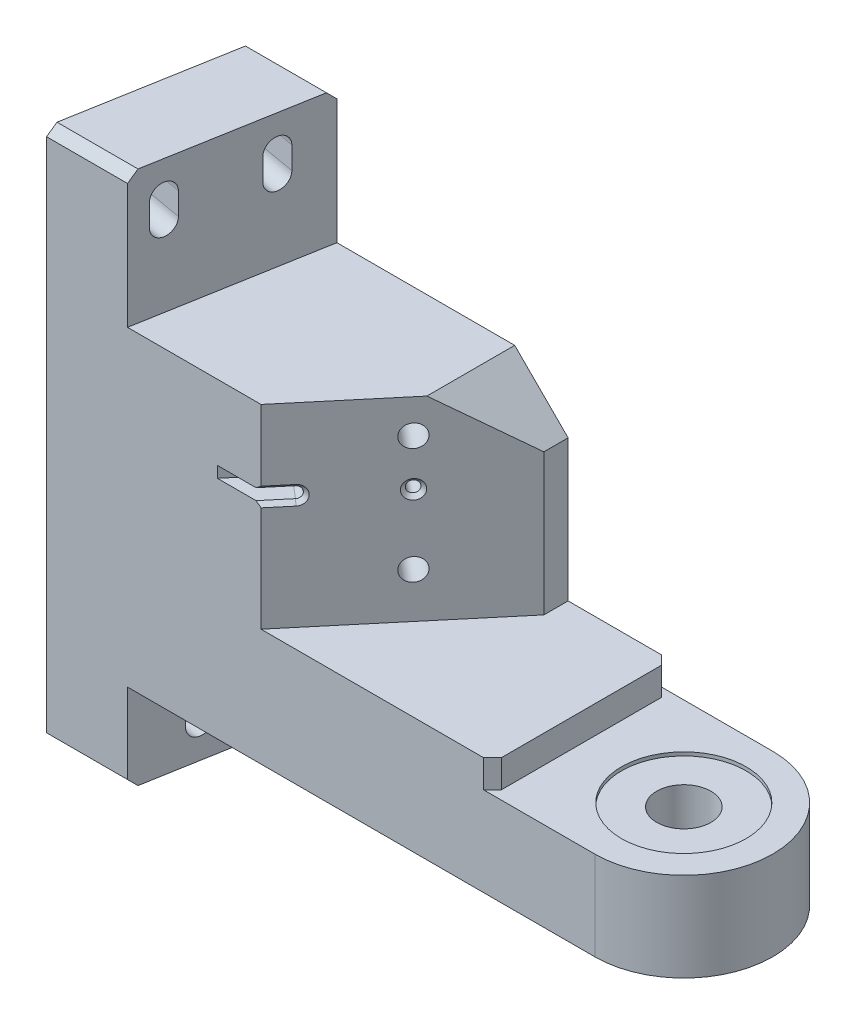
SolidWorks part; units mm, degrees
material "6061-T6 Al"
ref_plane "Front" through (0, 0, 0) normal (0, 0, 1) x (1, 0, 0)
ref_plane "Top" through (0, 0, 0) normal (0, 1, 0) x (1, 0, 0)
ref_plane "Right" through (0, 0, 0) normal (1, 0, 0) x (0, 0, -1)
sketch "Sketch1" plane through (0, 0, 0) normal (0, 1, 0) x (1, 0, 0)
  line L0 (-156.464, 0) -> (25.4, 0) construction
  line L1 (-156.464, 25.4) -> (25.4, 25.4)
  line L2 (-156.464, 25.4) -> (-156.464, -25.4)
  line L3 (-156.464, -25.4) -> (25.4, -25.4)
  line L4 (25.4, 25.4) -> (25.4, -25.4)
  dimension "D1" = 25.4
  dimension "D2" = 181.864
  dimension "D3" = 50.8
extrude "Extrude1" add sketch "Sketch1" along normal blind 152.4
sketch "Sketch2" plane through (0, 152.4, 0) normal (0, 1, 0) x (1, 0, 0)
  line L0 (-156.464, -25.4) -> (-156.464, 25.4)
  line L1 (-156.464, 25.4) -> (-147.5066, 25.4)
  line L2 (25.4, 25.4) -> (-156.464, 25.4) construction
  line L3 (-147.5066, 25.4) -> (-156.464, -25.4)
  dimension "D1" = 10
extrude "Extrude2" cut sketch "Sketch2" against normal through all
sketch "Sketch3" plane through (0, 152.4, 0) normal (0, 1, 0) x (1, 0, 0)
  line L0 (25.4, -25.4) -> (25.4, 25.4) construction
  line L1 (-156.464, -25.4) -> (25.4, -25.4) construction
  line L2 (25.4, 25.4) -> (-147.5066, 25.4) construction
  line L3 (25.4, -25.4) -> (25.4, 25.4)
  line L4 (-133.35, -25.4) -> (25.4, -25.4)
  line L5 (25.4, 25.4) -> (-124.3926, 25.4)
  line L6 (-124.3926, 25.4) -> (-133.35, -25.4)
  line L7 (-156.464, -25.4) -> (-147.5066, 25.4) construction
  dimension "D1" = 133.35
extrude "Extrude3" cut sketch "Sketch3" against normal blind 38.1
sketch "Sketch4" plane through (0, 114.3, 0) normal (0, 1, 0) x (1, 0, 0)
  line L1 (-133.35, -25.4) -> (25.4, -25.4) construction
  line L2 (25.4, 25.4) -> (-124.3926, 25.4) construction
  line L3 (25.4, -25.4) -> (25.4, 25.4) construction
  line L4 (25.4, -25.4) -> (-95.25, -25.4)
  line L5 (-58.42, 25.4) -> (25.4, 25.4)
  line L6 (-58.42, 25.4) -> (-58.42, 18.4923)
  line L7 (-58.42, 18.4923) -> (-95.25, -25.4)
  line L8 (25.4, -25.4) -> (25.4, 25.4)
  dimension "D1" = 130
  dimension "D2" = 58.42
  dimension "D3" = 95.25
extrude "Extrude4" cut sketch "Sketch4" against normal blind 55.5498
sketch "Sketch5" plane through (0, 58.7502, 0) normal (0, 1, 0) x (1, 0, 0)
  line L0 (-95.25, -25.4) -> (25.4, -25.4) construction
  line L1 (25.4, -25.4) -> (25.4, 25.4) construction
  line L2 (25.4, 25.4) -> (-58.42, 25.4) construction
  line L3 (-29.21, -25.4) -> (25.4, -25.4)
  line L4 (25.4, -25.4) -> (25.4, 25.4)
  line L5 (25.4, 25.4) -> (-29.21, 25.4)
  line L6 (-29.21, 25.4) -> (-29.21, -25.4)
  dimension "D1" = 29.21
extrude "Extrude5" cut sketch "Sketch5" against normal blind 7.9502
sketch "Sketch6" plane through (0, 0, 0) normal (0, -1, 0) x (1, 0, 0)
  line L0 (25.4, 25.4) -> (25.4, -25.4) construction
  line L1 (25.4, -25.4) -> (-147.5066, -25.4) construction
  line L2 (-156.464, 25.4) -> (25.4, 25.4) construction
  line L3 (25.4, 25.4) -> (25.4, -25.4)
  line L4 (25.4, -25.4) -> (-124.3926, -25.4)
  line L5 (-133.35, 25.4) -> (25.4, 25.4)
  line L7 (-124.3926, -25.4) -> (-133.35, 25.4)
extrude "Extrude6" cut sketch "Sketch6" against normal blind 25.4
sketch "Sketch7" plane through (-124.9853, 0, -22.0383) normal (0.9848, 0, 0.1736) x (0.1736, 0, -0.9848)
  line L0 (-39.2044, 142.9766) -> (-39.2044, 136.6266) construction
  line L1 (-35.6357, 142.9766) -> (-35.6357, 136.6266)
  line L2 (-42.7731, 142.9766) -> (-42.7731, 136.6266)
  line L3 (-48.1701, 0) -> (3.4136, 0) construction
  line L4 (-52.1838, 152.4) -> (-52.1838, 0) construction
  arc A0 (-35.6357, 142.9766) -> (-42.7731, 142.9766) centre (-39.2044, 142.9766) ccw
  arc A1 (-42.7731, 136.6266) -> (-35.6357, 136.6266) centre (-39.2044, 136.6266) ccw
  circle A2 centre (-39.2044, 139.8016) radius 3.5687 construction
  point P2 (-39.2044, 139.8016)
  dimension "D1" = 7.1374
  dimension "D2" = 6.35
  dimension "D3" = 139.8016
  dimension "D4" = 12.9794
extrude "Extrude7" cut sketch "Sketch7" against normal through all
pattern_linear "LPattern1" count 2 spacing 127 along (0, -1, 0) count 2 spacing 27.94 along (0.1736, 0, -0.9848) skipping (1, 0) of "Extrude7"
hole_wizard "1/4-20 Tapped Hole1" positions "Sketch9" profile "Sketch8" tap size "1/4-20" standard "Ansi Inch"
sketch "Sketch9" plane through (-43.3879, 0, -36.4068) normal (0.766, 0, 0.6428) x (0.6428, 0, -0.766)
  line L0 (-3.1307, 25.4) -> (-105.1733, 25.4) construction
  line L4 (-80.683, 58.7502) -> (-80.683, 114.3) construction
  point P0 (-49.822, 104.648)
  point P2 (-49.822, 71.628)
  dimension "D1" = 33.02
  dimension "D2" = 46.228
  dimension "D3" = 30.861
sketch "Sketch8" plane through (-75.4129, 104.648, 1.7591) normal (0, 1, 0) x (0.6428, 0, -0.766)
  line L0 (0, 0) -> (0, 18.0438)
  line L1 (0, 18.0438) -> (2.5527, 16.51)
  line L2 (2.5527, 16.51) -> (2.5527, 12.7)
  line L3 (2.5527, 12.7) -> (3.175, 12.7)
  line L4 (3.175, 12.7) -> (3.175, 0)
  line L5 (3.175, 0) -> (0, 0)
  line L10 (0, 18.0438) -> (-2.5527, 16.51) construction
  line L11 (0, -6.35) -> (0, 107.95) construction
  dimension "Tap Drill Dia." = 5.1054
  dimension "Tap Drill Depth" = 16.51
  dimension "Thread Major Dia." = 6.35
  dimension "Thread Depth" = 12.7
  dimension "Drill Angle" = 118
sketch "Sketch19" plane through (0, 25.4, 0) normal (0, -1, 0) x (1, 0, 0)
  line L4 (25.4, 25.4) -> (-133.35, 25.4)
  line L5 (-133.35, 25.4) -> (-124.3926, -25.4)
  line L6 (-124.3926, -25.4) -> (25.4, -25.4)
  line L7 (25.4, -25.4) -> (25.4, 25.4)
  line L8 (27.94, 25.4) -> (0, 25.4)
  line L10 (0, -25.4) -> (27.94, -25.4)
  line L11 (27.94, -25.4) -> (27.94, 25.4)
  arc A0 (0, -25.4) -> (0, 25.4) centre (0, 0) ccw
  dimension "D2" = 25.4
  dimension "D3" = 27.94
  dimension "D4" = 50.8
  dimension "D1" = 0
extrude "Extrude9" cut sketch "Sketch19" against normal through all
chamfer "Chamfer1" distance 2.54 angle 45 6 edges at (-29.21, 54.7751, 25.4) (-29.21, 54.7751, -25.4) (-135.9496, 152.4, -25.4) (-135.9496, 0, -25.4) (-144.907, 0, 25.4) (-144.907, 152.4, 25.4)
chamfer "Chamfer2" distance 15.24 angle 45 1 edges at (-58.42, 114.3, -21.9461)
sketch "Sketch20" plane through (-124.9853, 0, -22.0383) normal (0.9848, 0, 0.1736) x (0.1736, 0, -0.9848)
  line L0 (-30.3144, 15.9766) -> (-30.3144, 9.6266) construction
  line L1 (-26.7457, 15.9766) -> (-26.7457, 9.6266)
  line L2 (-33.8831, 15.9766) -> (-33.8831, 9.6266)
  line L3 (-11.2644, 9.6266) -> (-30.3144, 9.6266) construction
  line L4 (-11.2644, 15.9766) -> (-30.3144, 15.9766) construction
  arc A0 (-26.7457, 15.9766) -> (-33.8831, 15.9766) centre (-30.3144, 15.9766) ccw
  arc A1 (-33.8831, 9.6266) -> (-26.7457, 9.6266) centre (-30.3144, 9.6266) ccw
  arc A2 (-14.8331, 9.6266) -> (-7.6957, 9.6266) centre (-11.2644, 9.6266) ccw construction
  point P2 (-30.3144, 12.8016)
  dimension "D1" = 19.05
extrude "Extrude10" cut sketch "Sketch20" against normal through all
hole_wizard "SCREW THRU HOLE AND CBORE" positions "Sketch22" profile "Sketch21" counterbore size "5/8" standard "Ansi Inch" end condition through all
sketch "Sketch22" plane through (0, 50.8, 0) normal (0, 1, 0) x (-1, 0, 0)
  point P0 (0, 0)
sketch "Sketch21" plane through (0, 50.8, 0) normal (1, 0, 0) x (0, 0, 1)
  line L0 (0, 0) -> (0, 50.8)
  line L1 (0, 50.8) -> (7.7343, 50.8)
  line L3 (7.7343, 50.8) -> (7.7343, 1.016)
  line L4 (7.7343, 1.016) -> (17.78, 1.016)
  line L5 (17.78, 1.016) -> (17.78, 0)
  line L7 (17.78, 0) -> (0, 0)
  line L11 (0, -6.35) -> (0, 107.95) construction
  dimension "Thru Hole Dia." = 15.4686
  dimension "Thru Hole Depth" = 50.8
  dimension "C'Bore Dia." = 35.56
  dimension "C'Bore Depth" = 1.016
hole_wizard "1/8 (0.125) Diameter Hole1" positions "Sketch25" profile "Sketch24" hole size "1/8" standard "Ansi Inch"
sketch "Sketch25" plane through (-43.3879, 0, -36.4068) normal (0.766, 0, 0.6428) x (0.6428, 0, -0.766)
  line L0 (-80.683, 58.7502) -> (-80.683, 114.3) construction
  circle A0 centre (-49.822, 104.648) radius 2.5527 construction
  point P0 (-49.784, 91.4126)
  dimension "D1" = 13.2354
  dimension "D2" = 30.899
sketch "Sketch24" plane through (-75.3885, 91.4126, 1.73) normal (0, 1, 0) x (0.6428, 0, -0.766)
  line L0 (0, 0) -> (0, 10.4834)
  line L1 (0, 10.4834) -> (1.5951, 9.525)
  line L2 (1.5951, 9.525) -> (1.5951, 1.0719)
  line L3 (1.5951, 1.0719) -> (2.667, 0)
  line L5 (2.667, 0) -> (0, 0)
  line L6 (-1.5951, 1.0719) -> (-2.667, 0) construction
  line L10 (0, 10.4834) -> (-1.5951, 9.525) construction
  line L11 (0, -6.35) -> (0, 107.95) construction
  dimension "Hole Dia." = 3.1902
  dimension "Hole Depth" = 9.525
  dimension "Near C'Sink Dia." = 5.334
  dimension "Near C'Sink Angle" = 90
  dimension "Drill Angle" = 118
sketch "Sketch26" plane through (-43.3879, 0, -36.4068) normal (0.766, 0, 0.6428) x (0.6428, 0, -0.766)
  line L0 (-73.6092, 91.4126) -> (-92.6592, 91.4126) construction
  line L1 (-73.6092, 89.8175) -> (-92.6592, 89.8175)
  line L2 (-73.6092, 93.0077) -> (-92.6592, 93.0077)
  line L4 (-49.784, 91.4126) -> (-73.6092, 91.4126) construction
  arc A0 (-73.6092, 89.8175) -> (-73.6092, 93.0077) centre (-73.6092, 91.4126) ccw
  arc A1 (-92.6592, 93.0077) -> (-92.6592, 89.8175) centre (-92.6592, 91.4126) ccw
  circle A2 centre (-49.784, 91.4126) radius 1.5951 construction
  point P2 (-83.1342, 91.4126)
  dimension "D1" = 23.8252
  dimension "D2" = 19.05
extrude "Cut-Extrude1" cut sketch "Sketch26" against normal blind 9.525
chamfer "Chamfer3" distance 1.0795 angle 45 3 edges at (-92.9765, 89.8175, 22.6906) (-92.9765, 93.0077, 22.6906) (-89.6777, 91.4126, 18.7592)
